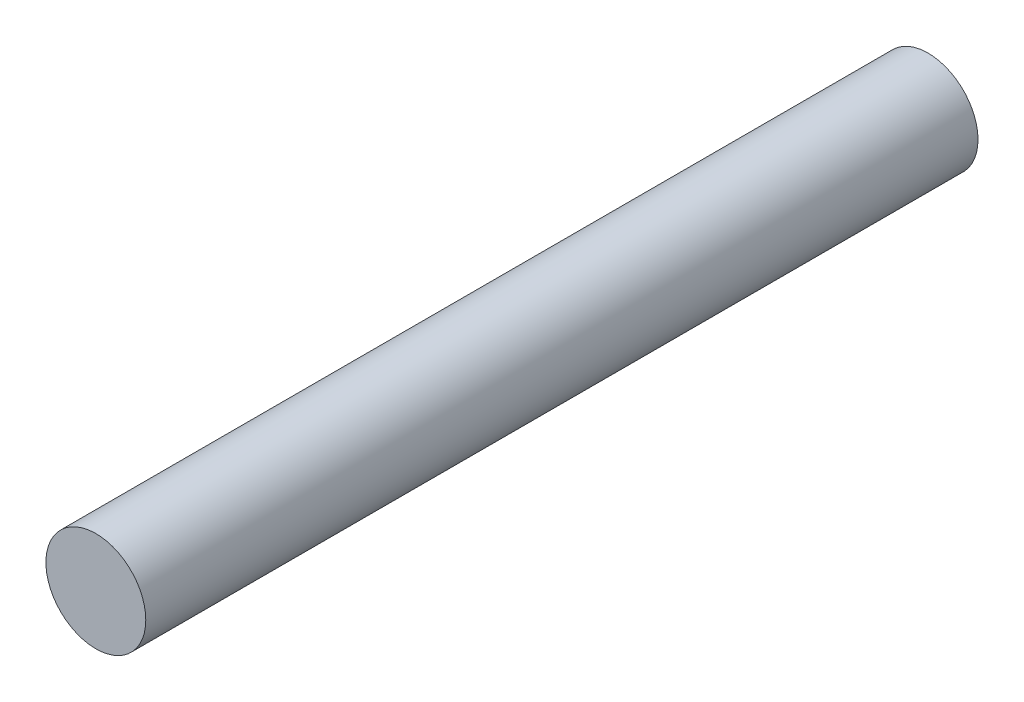
SolidWorks part; units mm, degrees
ref_plane "正面" through (0, 0, 0) normal (0, 0, 1) x (1, 0, 0)
ref_plane "平面" through (0, 0, 0) normal (0, 1, 0) x (1, 0, 0)
ref_plane "右側面" through (0, 0, 0) normal (1, 0, 0) x (0, 0, -1)
sketch "ｽｹｯﾁ1" plane through (0, 0, 0) normal (0, 0, 1) x (1, 0, 0)
  circle A0 centre (0, 0) radius 1.5
  dimension "D1" = 3
extrude "ﾎﾞｽ - 押し出し1" add sketch "ｽｹｯﾁ1" along normal blind 25
